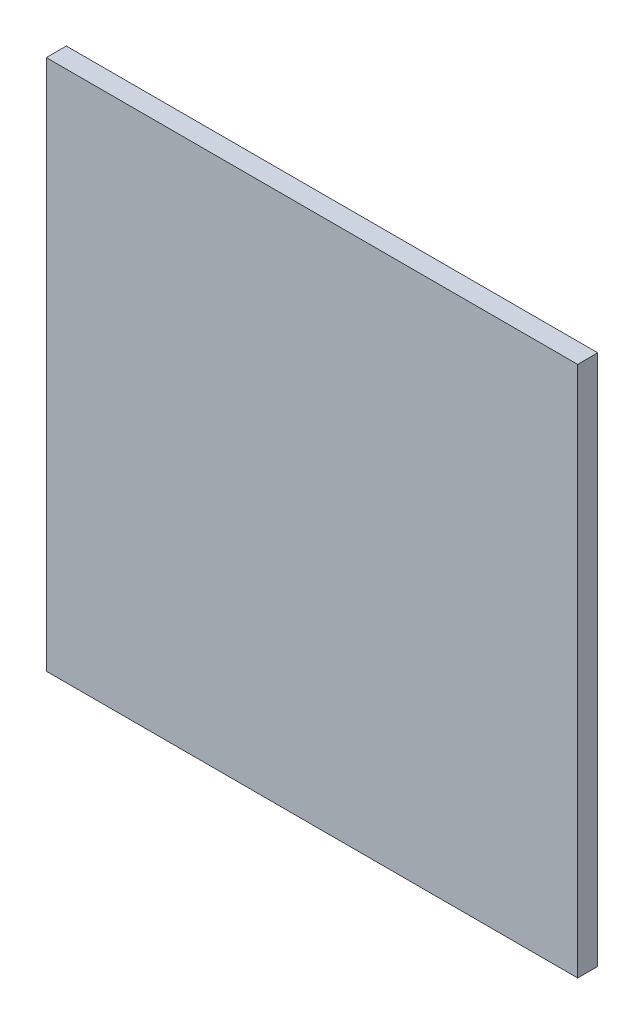
SolidWorks part; units mm, degrees
ref_plane "Front Plane" through (0, 0, 0) normal (0, 0, 1) x (1, 0, 0)
ref_plane "Top Plane" through (0, 0, 0) normal (0, 1, 0) x (1, 0, 0)
ref_plane "Right Plane" through (0, 0, 0) normal (1, 0, 0) x (0, 0, -1)
sketch "Sketch1" plane through (0, 0, 0) normal (0, 0, 1) x (1, 0, 0)
  line L1 (265, 265) -> (-265, 265)
  line L2 (265, 265) -> (265, -265)
  line L3 (265, -265) -> (-265, -265)
  line L4 (-265, 265) -> (-265, -265)
  line L5 (265, 265) -> (-265, -265) construction
  line L6 (265, -265) -> (-265, 265) construction
  point P0 (0, 0)
  dimension "D1" = 530
extrude "Boss-Extrude1" add sketch "Sketch1" along normal blind 20
